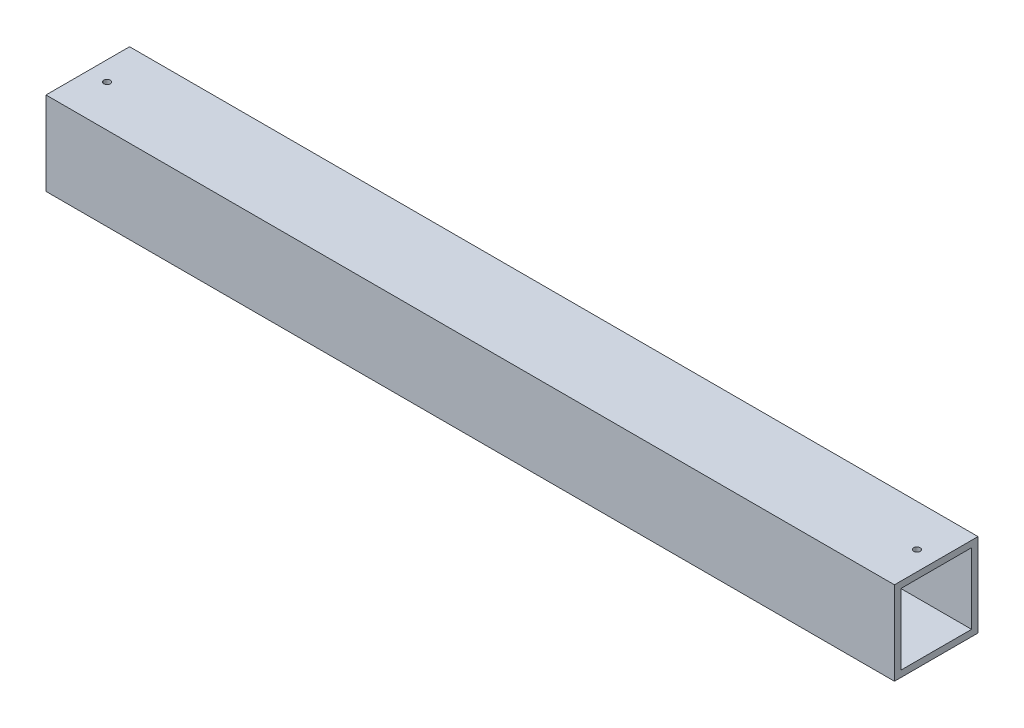
SolidWorks part; units mm, degrees
ref_plane "Front Plane" through (0, 0, 0) normal (0, 0, 1) x (1, 0, 0)
ref_plane "Top Plane" through (0, 0, 0) normal (0, 1, 0) x (1, 0, 0)
ref_plane "Right Plane" through (0, 0, 0) normal (1, 0, 0) x (0, 0, -1)
sketch "Sketch1" plane through (0, 0, 0) normal (0, 0, 1) x (1, 0, 0)
  line L1 (0, 0) -> (1676.4, 0)
  line L2 (0, 0) -> (0, 165.1)
  line L3 (0, 165.1) -> (1676.4, 165.1)
  line L4 (1676.4, 0) -> (1676.4, 165.1)
  dimension "D1" = 165.1
  dimension "D2" = 1676.4
extrude "Boss-Extrude1" add sketch "Sketch1" along normal blind 165.1
sketch "Sketch2" plane through (1676.4, 0, 0) normal (1, 0, 0) x (0, 0, -1)
  line L0 (0, 0) -> (0, 165.1) construction
  line L1 (-152.4, 12.7) -> (-12.7, 12.7)
  line L2 (-152.4, 12.7) -> (-152.4, 152.4)
  line L3 (-152.4, 152.4) -> (-12.7, 152.4)
  line L4 (-12.7, 12.7) -> (-12.7, 152.4)
  line L5 (-165.1, 0) -> (0, 0) construction
  dimension "D1" = 139.7
  dimension "D2" = 12.7
  dimension "D3" = 12.7
extrude "Cut-Extrude1" cut sketch "Sketch2" against normal up to surface (1676.4 mm away) up to face at (0, 82.55, 82.55)
sketch "Sketch3" plane through (0, 0, 0) normal (-1, 0, 0) x (0, 0, 1)
  line L0 (0, 165.1) -> (0, 0) construction
  line L1 (12.7, 12.7) -> (152.4, 12.7)
  line L2 (12.7, 12.7) -> (12.7, 152.4)
  line L3 (12.7, 152.4) -> (152.4, 152.4)
  line L4 (152.4, 12.7) -> (152.4, 152.4)
  line L5 (165.1, 165.1) -> (0, 165.1) construction
  dimension "D1" = 139.7
  dimension "D2" = 12.7
  dimension "D3" = 12.7
extrude "Cut-Extrude2" [suppressed] cut sketch "Sketch3" against normal blind 127
sketch "Sketch4" plane through (0, 165.1, 0) normal (0, 1, 0) x (1, 0, 0)
  line L0 (1676.4, -165.1) -> (1676.4, 0) construction
  line L2 (1676.4, -165.1) -> (0, -165.1) construction
  line L5 (0, -165.1) -> (0, 0) construction
  line L6 (1676.4, 0) -> (0, 0) construction
  circle A0 centre (38.1, -82.55) radius 6.35
  circle A1 centre (1638.3, -82.55) radius 6.35
  dimension "D1" = 12.7
  dimension "D2" = 12.7
  dimension "D3" = 38.1
  dimension "D5" = 38.1
  dimension "D6" = 82.55
  dimension "D4" = 82.55
extrude "Cut-Extrude3" cut sketch "Sketch4" against normal up to surface (12.7 mm away) up to face at (838.2, 152.4, 82.55)
